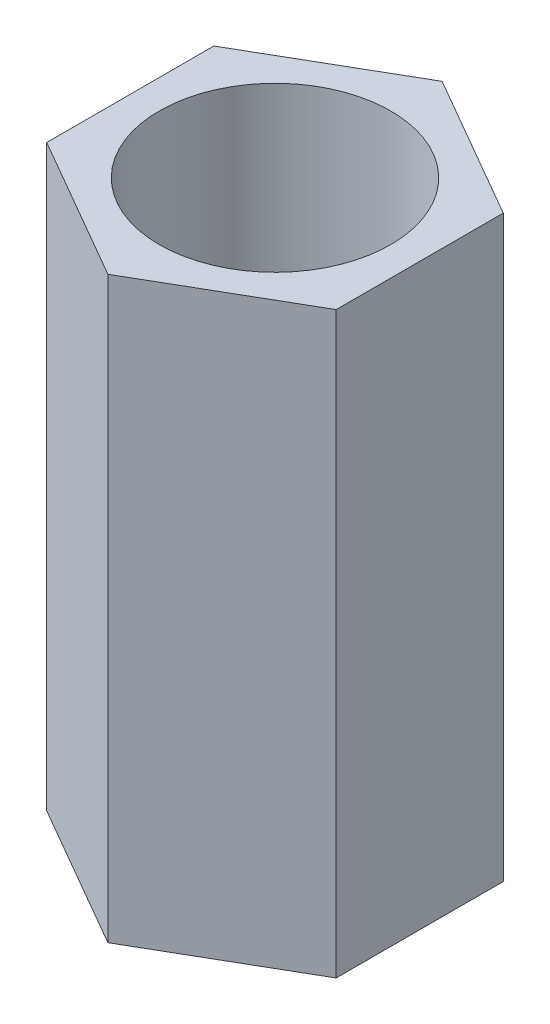
SolidWorks part; units mm, degrees
material "Brass"
ref_plane "Front Plane" through (0, 0, 0) normal (0, 0, 1) x (1, 0, 0)
ref_plane "Top Plane" through (0, 0, 0) normal (0, 1, 0) x (1, 0, 0)
ref_plane "Right Plane" through (0, 0, 0) normal (1, 0, 0) x (0, 0, -1)
other "Center of Mass"
sketch "Sketch1" plane through (0, 0, 0) normal (0, 1, 0) x (1, 0, 0)
  line L1 (0, 2.8868) -> (-2.5, 1.4434)
  line L2 (-2.5, 1.4434) -> (-2.5, -1.4434)
  line L3 (-2.5, -1.4434) -> (0, -2.8868)
  line L4 (0, -2.8868) -> (2.5, -1.4434)
  line L5 (2.5, -1.4434) -> (2.5, 1.4434)
  line L6 (2.5, 1.4434) -> (0, 2.8868)
  circle A1 centre (0, 0) radius 2
  circle A2 centre (0, 0) radius 2.5 construction
  dimension "D2" = 4
  dimension "D3" = 5
extrude "Boss-Extrude1" add sketch "Sketch1" along normal blind 10
